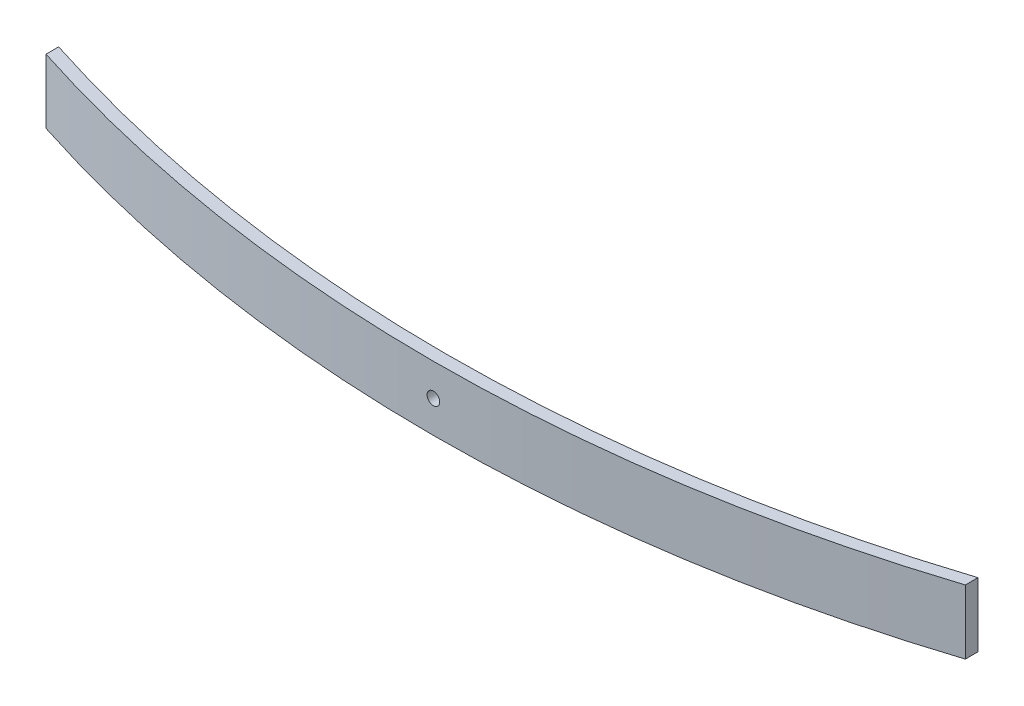
SolidWorks part; units mm, degrees
ref_plane "Front Plane" through (0, 0, 0) normal (0, 0, 1) x (1, 0, 0)
ref_plane "Top Plane" through (0, 0, 0) normal (0, 1, 0) x (1, 0, 0)
ref_plane "Right Plane" through (0, 0, 0) normal (1, 0, 0) x (0, 0, -1)
sketch "Sketch1" plane through (0, 0, 0) normal (0, 1, 0) x (1, 0, 0)
  line L0 (-630, 0) -> (630, 0) construction
  line L1 (-210.8013, -133) -> (245.5549, -133) construction
  line L2 (0, 0) -> (0, -133) construction
  line L3 (-602.5798, 17.4465) -> (-589.9243, 25.4988)
  line L4 (-616.835, -11.5296) -> (-605.5506, -21.4121)
  line L5 (616.835, -11.5296) -> (605.5506, -21.4121)
  line L6 (-630.0217, -47.5) -> (-630.0217, -62.5)
  line L7 (602.5798, 17.4465) -> (589.9243, 25.4988)
  line L8 (630.0217, -47.5) -> (630.0217, -62.5)
  line L9 (-545.0217, -92.3065) -> (-545.0217, -107.3065)
  line L10 (545.0217, -92.3065) -> (545.0217, -107.3065)
  arc A0 (-616.835, -11.5296) -> (-630, -17.5) centre (-630, 0) ccw
  arc A1 (630, -17.5) -> (616.835, -11.5296) centre (630, 0) ccw
  arc A2 (-630, -17.5) -> (630, -17.5) centre (0, 1642.9318) ccw
  arc A3 (-630.0011, -32.5) -> (630.0011, -32.5) centre (0, 1627.9379) ccw
  arc A4 (-605.5506, -21.4121) -> (-630.0011, -32.5) centre (-630, 0) ccw
  arc A5 (630.0011, -32.5) -> (605.5506, -21.4121) centre (630, 0) ccw
  arc A6 (-630.0217, -47.5) -> (630.0217, -47.5) centre (0, 1613.05) ccw
  arc A7 (630.0217, -47.5) -> (589.9243, 25.4988) centre (630, 0) ccw
  arc A8 (-589.9243, 25.4988) -> (-630.0217, -47.5) centre (-630, 0) ccw
  arc A9 (-630.0217, -62.5) -> (630.0217, -62.5) centre (0, 1598.05) ccw
  arc A10 (545.0217, -107.3065) -> (-545.0217, -107.3065) centre (0, 1583.05) cw
  point P5 (-630.0217, -47.5)
  point P6 (0, -163)
  point P10 (0, -133)
  point P13 (-630.0011, -32.5)
  point P14 (0, -148)
  point P15 (630.0011, -32.5)
  point P20 (630.0217, -47.5)
  point P27 (0, -178)
  point P37 (0, -193)
  point P40 (630.0217, -55)
  dimension "D4" = 35
  dimension "D5" = 35
  dimension "D9" = 15
  dimension "D12" = 15
  dimension "D1" = 133
  dimension "D2" = 630
  dimension "D3" = 630
  dimension "D6" = 15
  dimension "D7" = 15
  dimension "D8" = 15
  dimension "D10" = 15
  dimension "D11" = 15
  dimension "D13" = 15
  dimension "D14" = 15
  dimension "D15" = 15
  dimension "D16" = 85
  dimension "D17" = 15
  dimension "D18" = 15
  dimension "D19" = 85
sketch "Sketch5" plane through (0, 0, 0) normal (0, 0, 1) x (1, 0, 0)
  circle A0 centre (0, 38.1) radius 7.5
  dimension "D2" = 15
  dimension "D1" = 38.1
sketch "Sketch6" plane through (0, 0, 0) normal (0, 0, 1) x (1, 0, 0)
  circle A0 centre (0, 38.1) radius 7.5
sketch "Sketch7" plane through (0, 0, 0) normal (0, 0, 1) x (1, 0, 0)
  circle A0 centre (0, 38.1) radius 7.5
extrude "Boss-Extrude1" add sketch "Sketch1" along normal blind 76.2 contours A10 L10 A9 L9
sketch "Sketch8" plane through (0, 0, 0) normal (0, 0, 1) x (1, 0, 0)
  circle A0 centre (0, 38.1) radius 7.5
extrude "Cut-Extrude1" cut sketch "Sketch8" along normal through all
